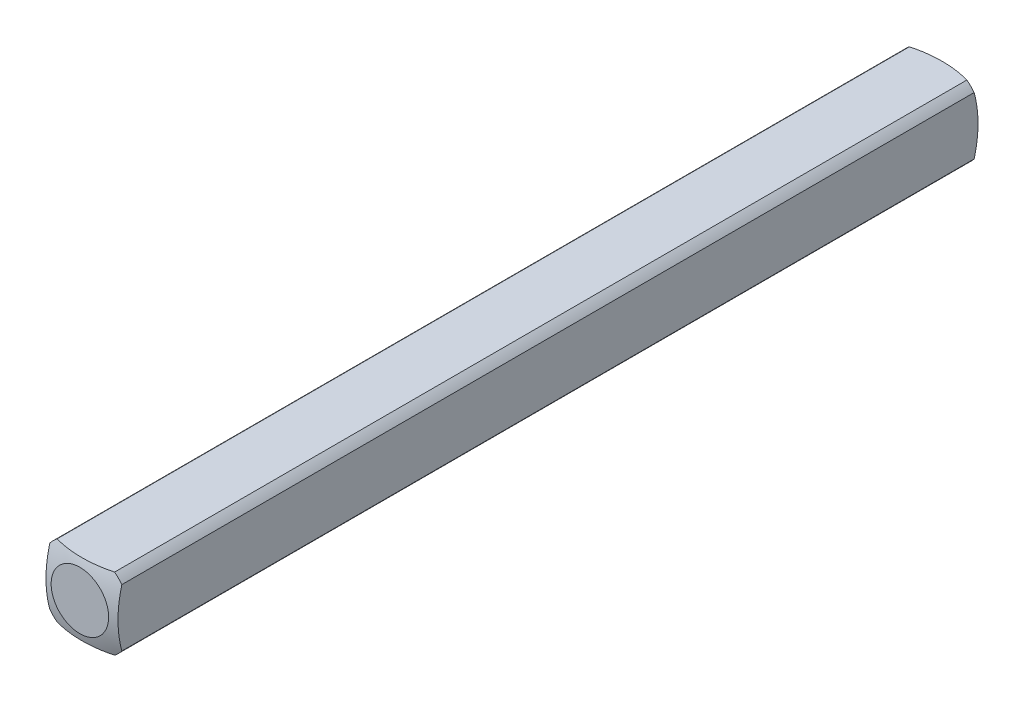
SolidWorks part; units mm, degrees
material "Custom Plastic"
ref_plane "Front Plane" through (0, 0, 0) normal (0, 0, 1) x (1, 0, 0)
ref_plane "Top Plane" through (0, 0, 0) normal (0, 1, 0) x (1, 0, 0)
ref_plane "Right Plane" through (0, 0, 0) normal (1, 0, 0) x (0, 0, -1)
sketch "Sketch1" plane through (0, 0, 0) normal (0, 0, 1) x (1, 0, 0)
  line L0 (-1.5875, -1.5875) -> (1.5875, 1.5875) construction
  line L1 (-1.5875, -1.5875) -> (1.5875, -1.5875)
  line L2 (-1.5875, -1.5875) -> (-1.5875, 1.5875)
  line L3 (-1.5875, 1.5875) -> (1.5875, 1.5875)
  line L4 (1.5875, -1.5875) -> (1.5875, 1.5875)
  dimension "D1" = 3.175
extrude "Boss-Extrude1" add sketch "Sketch1" along normal blind 19.05
sketch "Sketch2" plane through (0, 0, 0) normal (0, 0, -1) x (-1, 0, 0)
  circle A0 centre (0, 0) radius 2.032
  dimension "D1" = 4.064
extrude "Cut-Extrude1" cut sketch "Sketch2" against normal through all flip side to cut
ref_axis "Axis1" through (0, 0, 19.05) along (0, 0, -1)
sketch "Sketch3" plane through (0, 0, 0) normal (0, 1, 0) x (1, 0, 0)
  line L1 (-5.0537, -4.4027) -> (-5.0537, 5.7405)
  line L2 (-5.0537, 5.7405) -> (0, 5.7405)
  line L5 (0, -19.05) -> (0, 0) construction
  line L8 (0, 0.1609) -> (0, 5.7405)
  arc A0 (-5.0537, -4.4027) -> (0, 0.1609) centre (0, -4.9191) cw
  dimension "D1" = 5.08
revolve "Cut-Revolve1" cut sketch "Sketch3" angle 360 about axis through (0, 0, 19.05) along (0, 0, -1)
mirror "Mirror1" about plane through (0, 0, 19.05) normal (0, 0, -1) of bodies 103
